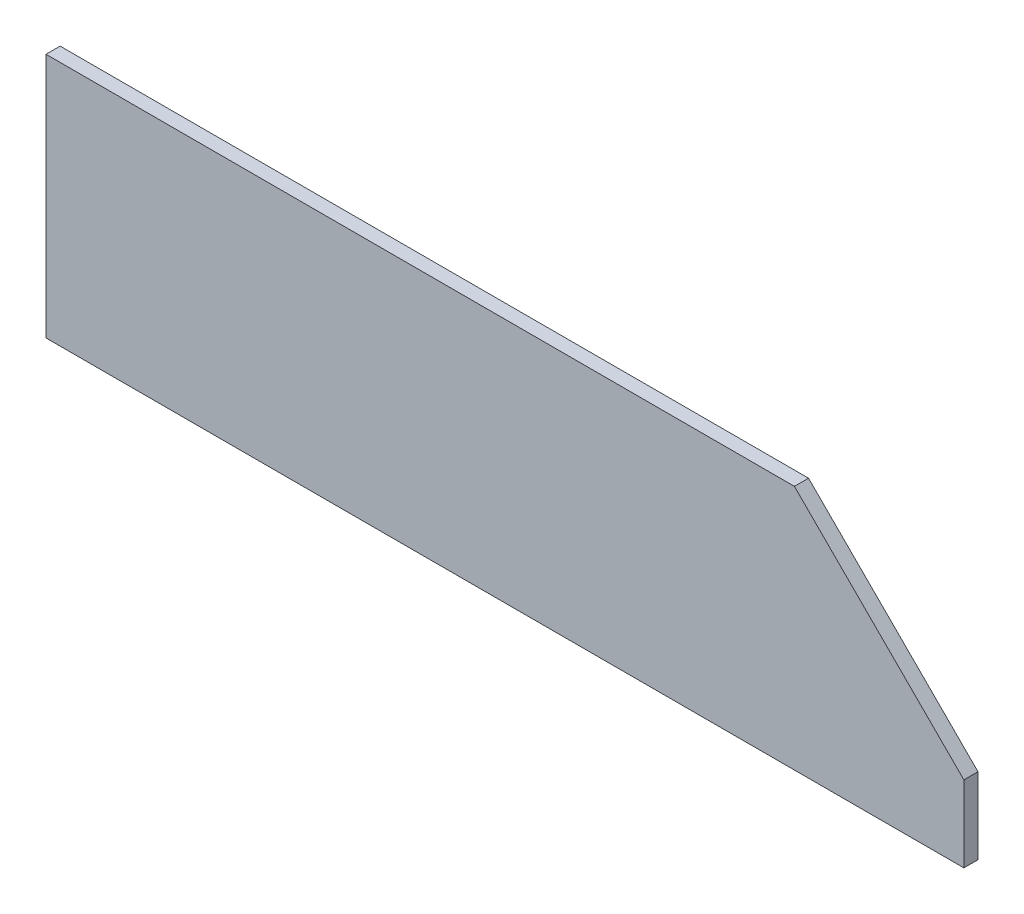
SolidWorks part; units mm, degrees
ref_plane "Front Plane" through (0, 0, 0) normal (0, 0, 1) x (1, 0, 0)
ref_plane "Top Plane" through (0, 0, 0) normal (0, 1, 0) x (1, 0, 0)
ref_plane "Right Plane" through (0, 0, 0) normal (1, 0, 0) x (0, 0, -1)
sketch "Sketch1" plane through (0, 0, 0) normal (0, 1, 0) x (1, 0, 0)
  line L1 (-162.5, 2.5) -> (162.5, 2.5)
  line L2 (-162.5, 2.5) -> (-162.5, -2.5)
  line L3 (-162.5, -2.5) -> (162.5, -2.5)
  line L4 (162.5, 2.5) -> (162.5, -2.5)
  line L5 (-162.5, 2.5) -> (162.5, -2.5) construction
  line L6 (-162.5, -2.5) -> (162.5, 2.5) construction
  point P0 (0, 0)
extrude "Boss-Extrude1" add sketch "Sketch1" along normal blind 87
chamfer "Chamfer1" distance 60 angle 45 1 edges at (162.5, 87, 0)
